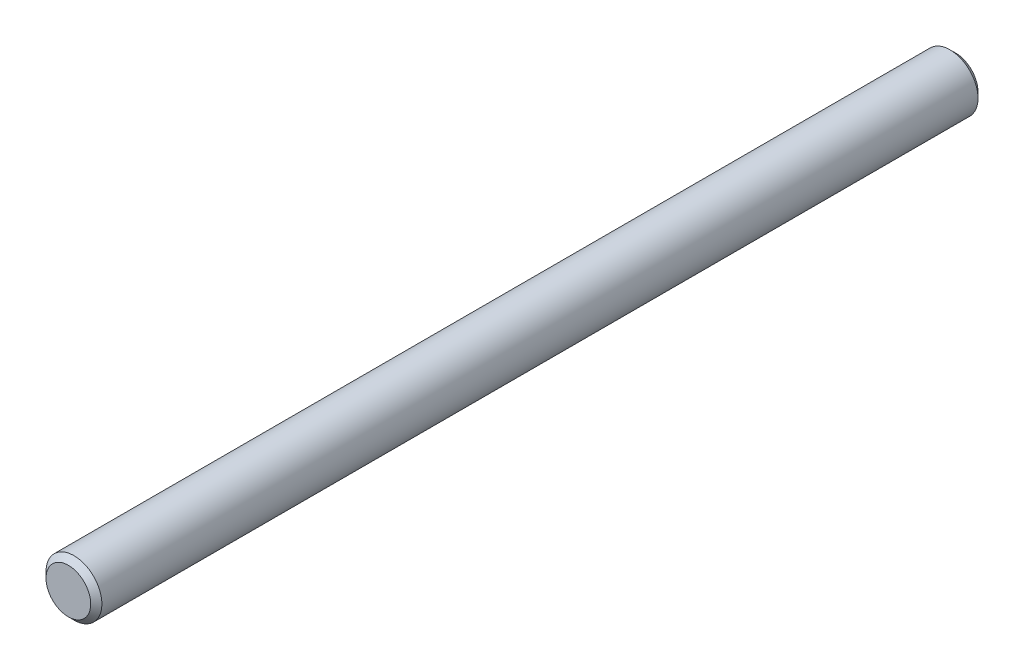
SolidWorks part; units mm, degrees
ref_plane "Front" through (0, 0, 0) normal (0, 0, 1) x (1, 0, 0)
ref_plane "Top" through (0, 0, 0) normal (0, 1, 0) x (1, 0, 0)
ref_plane "Right" through (0, 0, 0) normal (1, 0, 0) x (0, 0, -1)
sketch "Sketch1" plane through (0, 0, 0) normal (0, 0, 1) x (1, 0, 0)
  circle A0 centre (0, 0) radius 4.7625
  dimension "dia" = 9.525
extrude "Extrude1" add sketch "Sketch1" along normal mid plane 151.2
chamfer "Chamfer1" distance 0.9525 angle 45 2 edges at (4.7625, 0, -75.6) (4.7625, 0, 75.6)
sketch "Sketch2" plane through (0, 0, 0) normal (1, 0, 0) x (0, 0, -1)
  line L0 (-74.6475, 4.7625) -> (-69.6475, 4.7625) construction
  line L1 (74.6475, 4.7625) -> (-74.6475, 4.7625) construction
  line L2 (-69.6475, 4.7625) -> (-69.6475, -4.7625) construction
  line L3 (-74.6475, -4.7625) -> (74.6475, -4.7625) construction
  point P0 (-74.6475, 4.7625)
  point P1 (74.6475, 4.7625)
  dimension "D1" = 5
sketch "Sketch3" plane through (0, 0, 0) normal (0, 1, 0) x (1, 0, 0)
  line L0 (0, -75.6) -> (0, -70.6)
  line L1 (3.81, -75.6) -> (-3.81, -75.6) construction
  line L2 (-4.7625, -74.6475) -> (-3.81, -75.6) construction
  line L3 (-3.81, -70.6) -> (4.7625, -70.6) construction
  line L4 (4.7625, -74.6475) -> (4.7625, 74.6475) construction
  point P3 (4.7625, -70.6)
  point P9 (-3.81, -70.6)
  point P12 (-3.81, -70.6)
  dimension "D1" = 5
equation "\"D1@Chamfer1\" = \"dia@Sketch1\" * .1"
